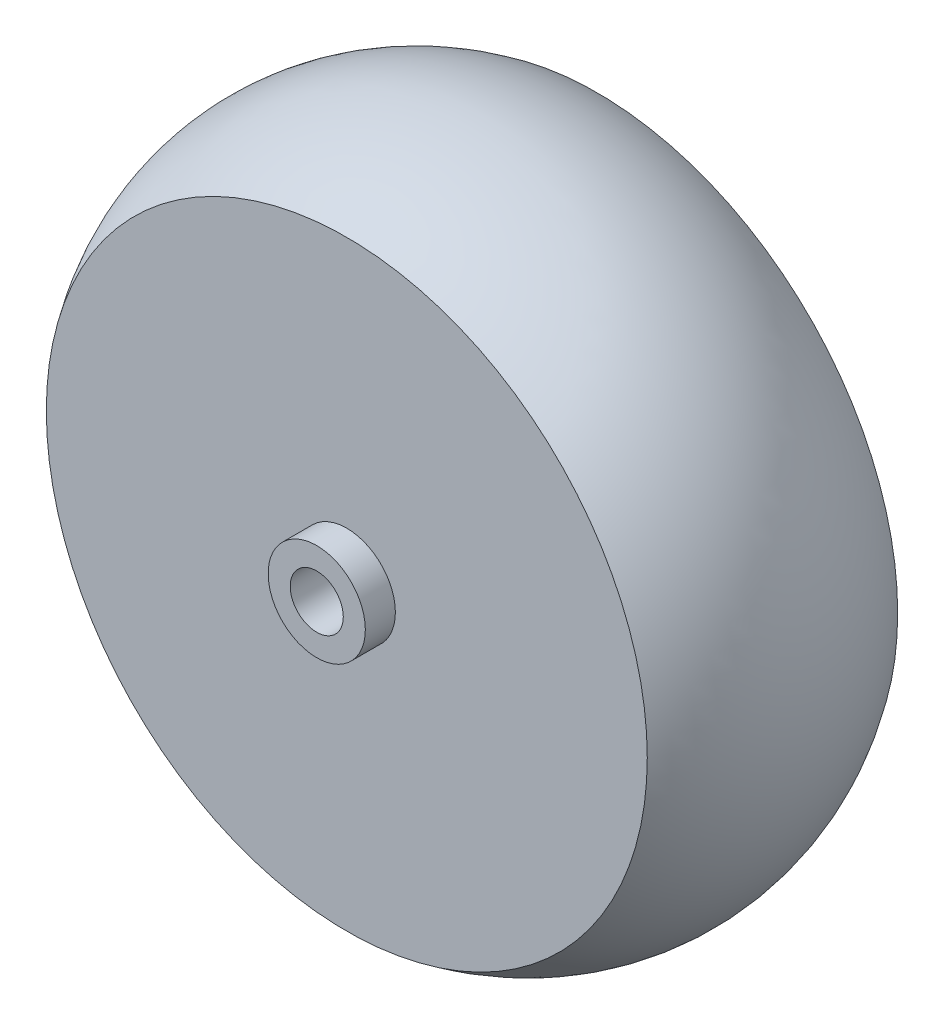
SolidWorks part; units mm, degrees
ref_plane "前视基准面" through (0, 0, 0) normal (0, 0, 1) x (1, 0, 0)
ref_plane "上视基准面" through (0, 0, 0) normal (0, 1, 0) x (1, 0, 0)
ref_plane "右视基准面" through (0, 0, 0) normal (1, 0, 0) x (0, 0, -1)
sketch "草图2" plane through (0, 0, 0) normal (0, 1, 0) x (1, 0, 0)
  line L0 (0, 0) -> (0, 28)
  line L1 (0, 28) -> (30, 28)
  line L2 (0, 0) -> (4.85, 0)
  line L3 (4.85, 0) -> (4.85, 3)
  line L4 (4.85, 3) -> (30, 3)
  line L5 (30, 28) -> (30, 3) construction
  line L6 (30, 15.5) -> (12.4688, 15.5) construction
  arc A1 (30, 3) -> (30, 28) centre (12.4688, 15.5) ccw
  point P8 (34, 15.5)
  dimension "D1" = 25
  dimension "D2" = 30
  dimension "D3" = 28
  dimension "D4" = 4.85
  dimension "D6" = 34
revolve "旋转1" add sketch "草图2" angle 360 about L0
sketch "草图3" plane through (0, 0, 0) normal (0, 0, 1) x (1, 0, 0)
  line L0 (0, 0) -> (1.6522, 0) construction
  line L1 (1.99, 1.75) -> (-1.99, 1.75)
  line L2 (1.99, -1.75) -> (-1.99, -1.75)
  arc A0 (-1.99, 1.75) -> (-1.99, -1.75) centre (0, 0) ccw
  arc A1 (1.99, -1.75) -> (1.99, 1.75) centre (0, 0) ccw
  dimension "D1" = 5.3
  dimension "D2" = 3.5
extrude "切除-拉伸1" cut sketch "草图3" against normal blind 10
sketch "草图4" plane through (0, 0, 0) normal (0, 0, 1) x (1, 0, 0)
  circle A0 centre (0, 0) radius 2.65
extrude "切除-拉伸2" cut sketch "草图4" against normal blind 5
